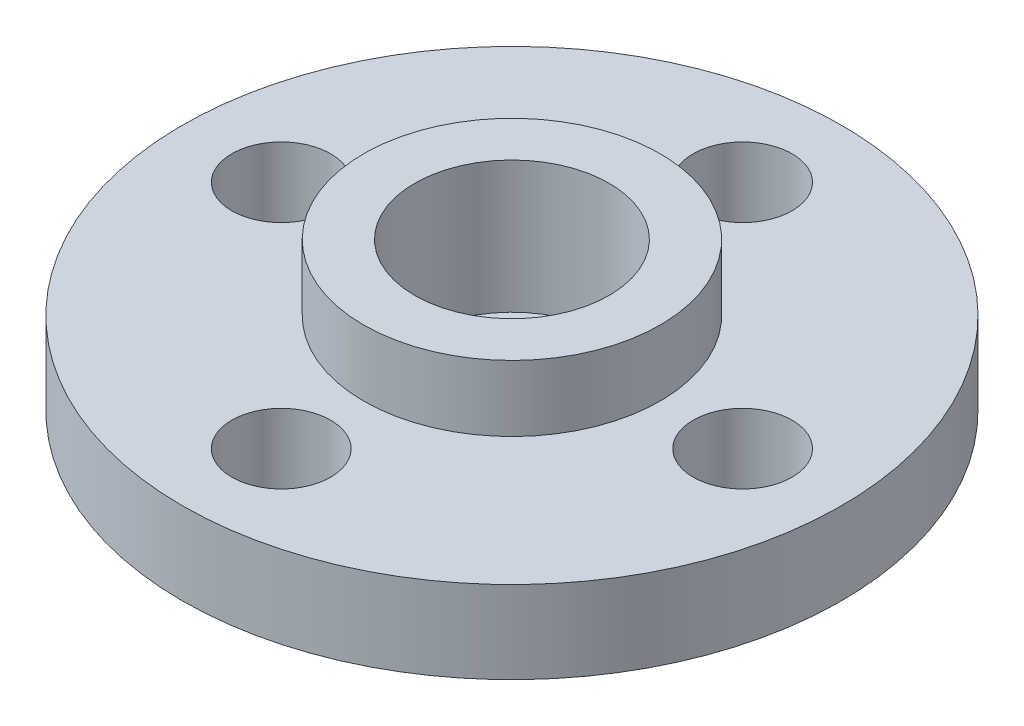
SolidWorks part; units mm, degrees
ref_plane "Ön Düzlem" through (0, 0, 0) normal (0, 0, 1) x (1, 0, 0)
ref_plane "Üst Düzlem" through (0, 0, 0) normal (0, 1, 0) x (1, 0, 0)
ref_plane "Sağ Düzlem" through (0, 0, 0) normal (1, 0, 0) x (0, 0, -1)
sketch "Çizim1" plane through (0, 0, 0) normal (0, 1, 0) x (1, 0, 0)
  circle A0 centre (0, 0) radius 10
  circle A1 centre (0, 7) radius 1.5
  circle A2 centre (7, 0) radius 1.5
  circle A3 centre (0, -7) radius 1.5
  circle A4 centre (-7, 0) radius 1.5
  point P14 (0, 0)
  dimension "D1" = 20
  dimension "D2" = 3
  dimension "D3" = 7
  dimension "D4" = 4
extrude "Yükseklik-Ekstrüzyon1" add sketch "Çizim1" along normal blind 2.5
sketch "Çizim2" plane through (0, 2.5, 0) normal (0, 1, 0) x (1, 0, 0)
  circle A0 centre (0, 0) radius 4.5
  circle A1 centre (0, 0) radius 2.95
  dimension "D1" = 9
  dimension "D2" = 5.9
extrude "Yükseklik-Ekstrüzyon2" add sketch "Çizim2" along normal blind 2
sketch "Çizim3" plane through (0, 2.5, 0) normal (0, 1, 0) x (1, 0, 0)
  circle A0 centre (0, 0) radius 1.6
  dimension "D1" = 3.2
extrude "Kes-Ekstrüzyon1" cut sketch "Çizim3" against normal through all
sketch "Çizim4" plane through (0, 2.5, 0) normal (0, 1, 0) x (1, 0, 0)
  circle A0 centre (0, 0) radius 1.6 construction
  circle A1 centre (0, 0) radius 2.95
  circle A2 centre (0, 0) radius 2.95
  circle A3 centre (0, 0) radius 1.6
  dimension "D1" = 0
extrude "Kes-Ekstrüzyon2" cut sketch "Çizim4" against normal blind 2
